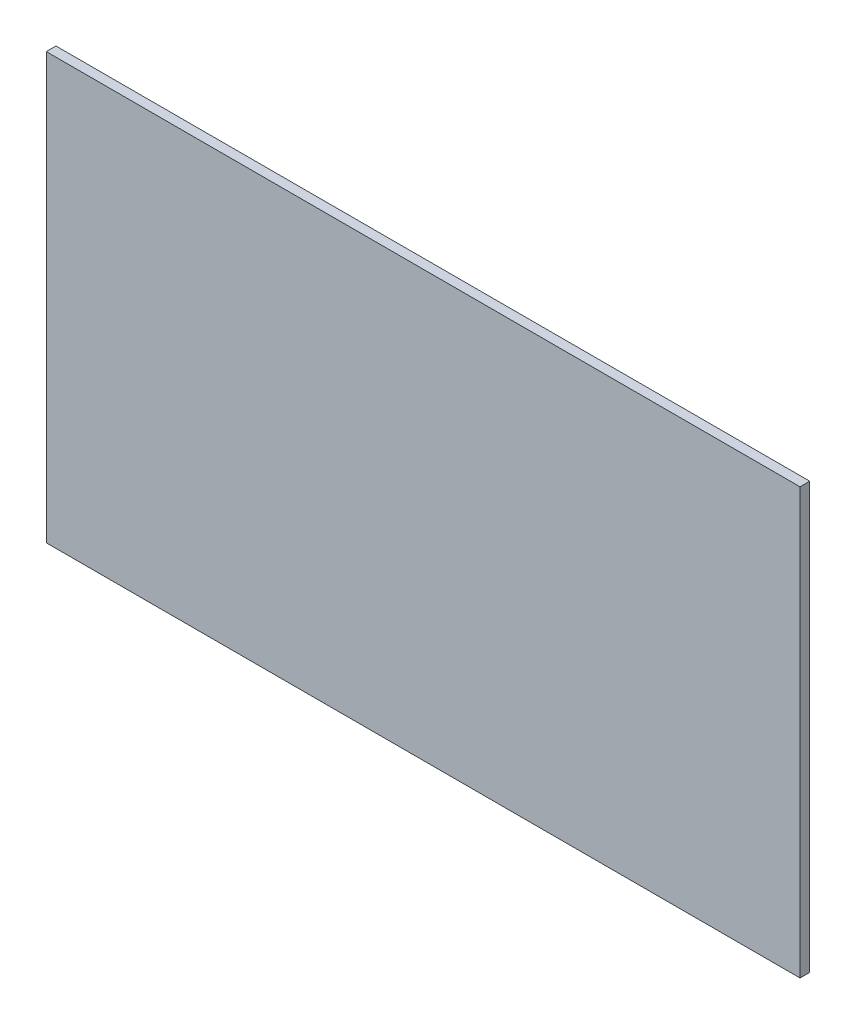
SolidWorks part; units mm, degrees
ref_plane "Front Plane" through (0, 0, 0) normal (0, 0, 1) x (1, 0, 0)
ref_plane "Top Plane" through (0, 0, 0) normal (0, 1, 0) x (1, 0, 0)
ref_plane "Right Plane" through (0, 0, 0) normal (1, 0, 0) x (0, 0, -1)
sketch "Sketch1" plane through (0, 0, 0) normal (0, 0, 1) x (1, 0, 0)
  line L0 (108, -131.5) -> (233, -131.5) construction
  line L1 (0, 0) -> (233, 0)
  line L2 (0, 0) -> (0, -131.5)
  line L3 (0, -131.5) -> (233, -131.5)
  line L4 (233, 0) -> (233, -131.5)
  dimension "D1" = 233
extrude "Boss-Extrude1" add sketch "Sketch1" along normal blind 3
